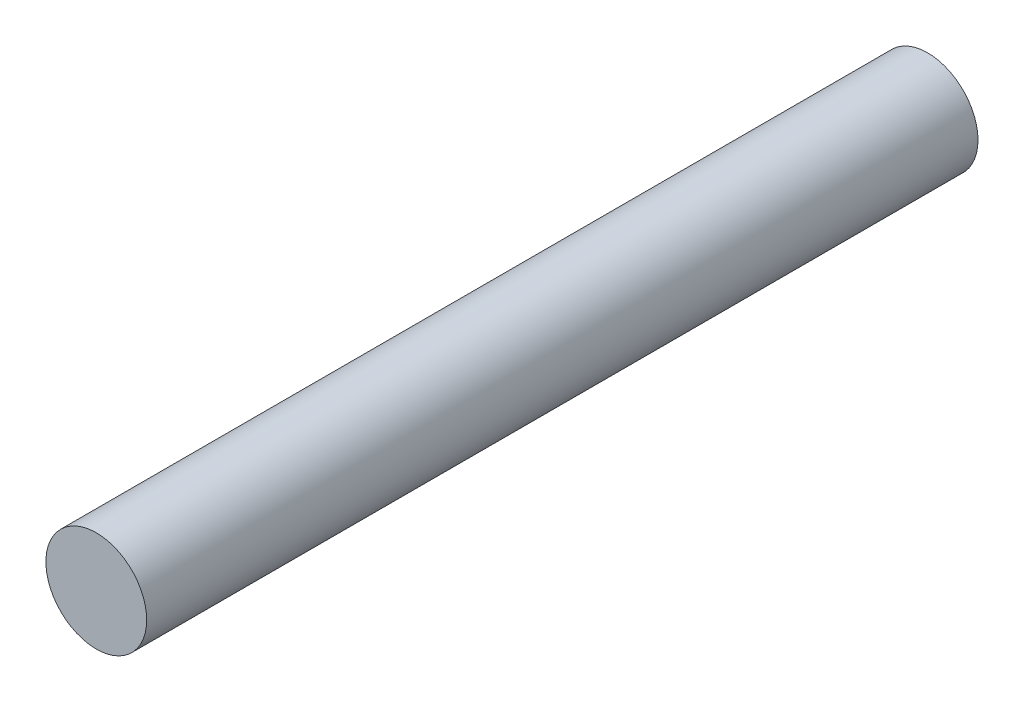
SolidWorks part; units mm, degrees
ref_plane "Plano frontal" through (0, 0, 0) normal (0, 0, 1) x (1, 0, 0)
ref_plane "Plano superior" through (0, 0, 0) normal (0, 1, 0) x (1, 0, 0)
ref_plane "Plano direito" through (0, 0, 0) normal (1, 0, 0) x (0, 0, -1)
sketch "Esboço1" plane through (0, 0, 0) normal (0, 0, 1) x (1, 0, 0)
  circle A0 centre (0, 0) radius 120
extrude "Ressalto-extrusão1" add sketch "Esboço1" along normal blind 1980
